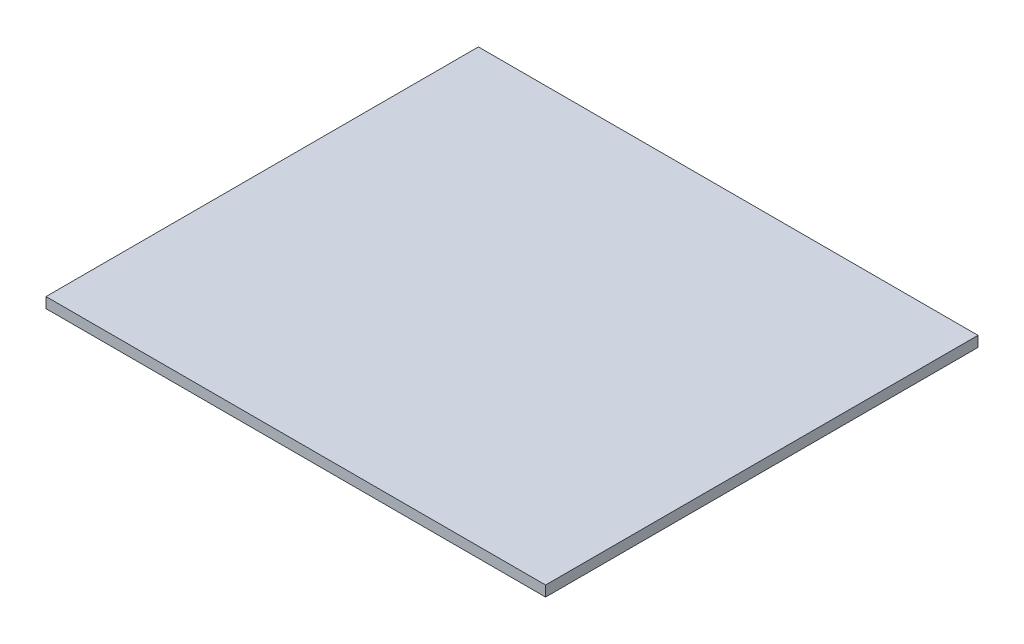
SolidWorks part; units mm, degrees
material "Custom Plastic"
ref_plane "Front Plane" through (0, 0, 0) normal (0, 0, 1) x (1, 0, 0)
ref_plane "Top Plane" through (0, 0, 0) normal (0, 1, 0) x (1, 0, 0)
ref_plane "Right Plane" through (0, 0, 0) normal (1, 0, 0) x (0, 0, -1)
sketch "Sketch1" plane through (0, 0, 0) normal (0, 1, 0) x (1, 0, 0)
  line L1 (-59.5, -51.5) -> (59.5, -51.5)
  line L2 (-59.5, -51.5) -> (-59.5, 51.5)
  line L3 (-59.5, 51.5) -> (59.5, 51.5)
  line L4 (59.5, -51.5) -> (59.5, 51.5)
  line L5 (-59.5, -51.5) -> (59.5, 51.5) construction
  line L6 (-59.5, 51.5) -> (59.5, -51.5) construction
  point P0 (0, 0)
  dimension "D1" = 119
  dimension "D2" = 103
extrude "Boss-Extrude1" add sketch "Sketch1" along normal blind 2.5
ref_plane "Plane1" through (0, 0, 0) normal (0, 0, -1) x (-1, 0, 0)
ref_plane "Plane2" through (0, 0, 0) normal (1, 0, 0) x (0, 0, -1)
